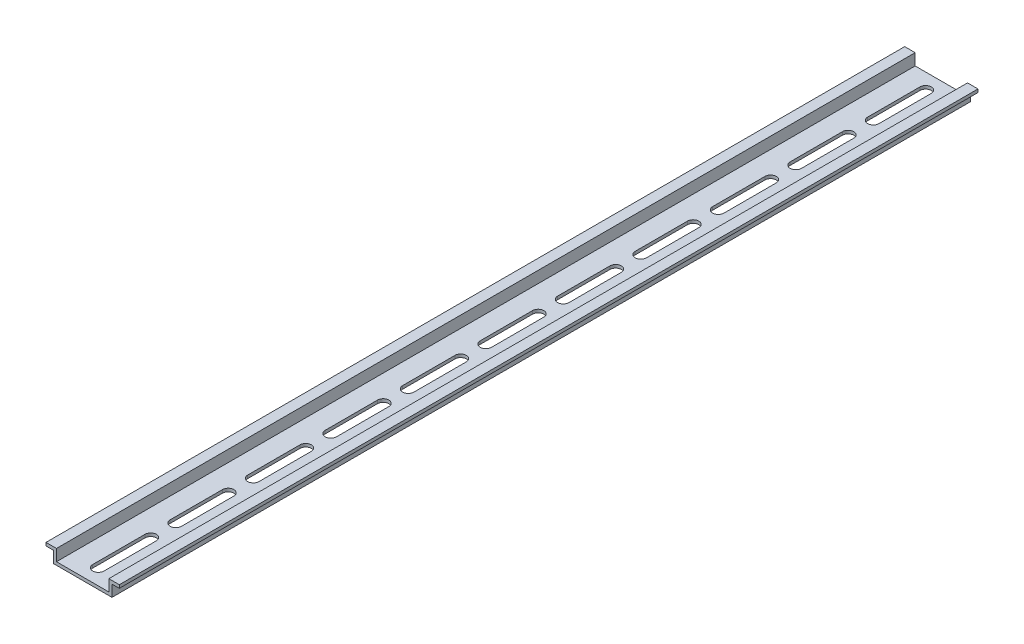
SolidWorks part; units mm, degrees
ref_plane "Alzado" through (0, 0, 0) normal (0, 0, 1) x (1, 0, 0)
ref_plane "Planta" through (0, 0, 0) normal (0, 1, 0) x (1, 0, 0)
ref_plane "Vista lateral" through (0, 0, 0) normal (1, 0, 0) x (0, 0, -1)
ref_plane "Plano1" through (0, -1.5, 0) normal (0, -1, 0) x (1, 0, 0)
sketch "Croquis1" plane through (0, -1.5, 0) normal (0, -1, 0) x (1, 0, 0)
  line L0 (-17.5, 0) -> (17.5, 0)
  line L1 (17.5, 0) -> (17.5, 410)
  line L2 (17.5, 410) -> (-17.5, 410)
  line L3 (-17.5, 410) -> (-17.5, 0)
extrude "Saliente-Extruir1" add sketch "Croquis1" against normal blind 7
sketch "Croquis2" plane through (0, 0, 410) normal (0, 0, 1) x (1, 0, 0)
  line L0 (-12.5, 5.5) -> (-12.5, 0)
  line L1 (-12.5, 0) -> (12.5, 0)
  line L2 (12.5, 0) -> (12.5, 5.5)
  line L3 (12.5, 5.5) -> (-12.5, 5.5)
extrude "Cortar-Extruir1" cut sketch "Croquis2" against normal through all
sketch "Croquis3" plane through (0, 0, 410) normal (0, 0, 1) x (1, 0, 0)
  line L0 (17.5, -1.5) -> (17.5, 4)
  line L1 (17.5, 4) -> (14, 4)
  line L2 (14, 4) -> (14, -1.5)
  line L3 (14, -1.5) -> (17.5, -1.5)
extrude "Cortar-Extruir2" cut sketch "Croquis3" against normal through all
sketch "Croquis4" plane through (0, 0, 410) normal (0, 0, 1) x (1, 0, 0)
  line L0 (-17.5, -1.5) -> (-14, -1.5)
  line L1 (-14, -1.5) -> (-14, 4)
  line L2 (-14, 4) -> (-17.5, 4)
  line L3 (-17.5, 4) -> (-17.5, -1.5)
extrude "Cortar-Extruir3" cut sketch "Croquis4" against normal through all
sketch "Croquis5" plane through (0, 0, 0) normal (0, 1, 0) x (-1, 0, 0)
  line L0 (-2.7, 402.5) -> (-2.7, 377.5)
  line L1 (2.7, 377.5) -> (2.7, 402.5)
  arc A0 (2.7, 402.5) -> (-2.7, 402.5) centre (0, 402.5) ccw
  arc A1 (-2.7, 377.5) -> (2.7, 377.5) centre (0, 377.5) ccw
extrude "Cortar-Extruir4" cut sketch "Croquis5" against normal through all
sketch "Croquis6" plane through (0, 0, 0) normal (0, 1, 0) x (-1, 0, 0)
  line L0 (-2.7, 365.5) -> (-2.7, 340.5)
  line L1 (2.7, 340.5) -> (2.7, 365.5)
  arc A0 (2.7, 365.5) -> (-2.7, 365.5) centre (0, 365.5) ccw
  arc A1 (-2.7, 340.5) -> (2.7, 340.5) centre (0, 340.5) ccw
extrude "Cortar-Extruir5" cut sketch "Croquis6" against normal through all
sketch "Croquis7" plane through (0, 0, 0) normal (0, 1, 0) x (-1, 0, 0)
  line L0 (-2.7, 328.5) -> (-2.7, 303.5)
  line L1 (2.7, 303.5) -> (2.7, 328.5)
  arc A0 (2.7, 328.5) -> (-2.7, 328.5) centre (0, 328.5) ccw
  arc A1 (-2.7, 303.5) -> (2.7, 303.5) centre (0, 303.5) ccw
extrude "Cortar-Extruir6" cut sketch "Croquis7" against normal through all
sketch "Croquis8" plane through (0, 0, 0) normal (0, 1, 0) x (-1, 0, 0)
  line L0 (-2.7, 291.5) -> (-2.7, 266.5)
  line L1 (2.7, 266.5) -> (2.7, 291.5)
  arc A0 (2.7, 291.5) -> (-2.7, 291.5) centre (0, 291.5) ccw
  arc A1 (-2.7, 266.5) -> (2.7, 266.5) centre (0, 266.5) ccw
extrude "Cortar-Extruir7" cut sketch "Croquis8" against normal through all
sketch "Croquis9" plane through (0, 0, 0) normal (0, 1, 0) x (-1, 0, 0)
  line L0 (-2.7, 254.5) -> (-2.7, 229.5)
  line L1 (2.7, 229.5) -> (2.7, 254.5)
  arc A0 (2.7, 254.5) -> (-2.7, 254.5) centre (0, 254.5) ccw
  arc A1 (-2.7, 229.5) -> (2.7, 229.5) centre (0, 229.5) ccw
extrude "Cortar-Extruir8" cut sketch "Croquis9" against normal through all
sketch "Croquis10" plane through (0, 0, 0) normal (0, 1, 0) x (-1, 0, 0)
  line L0 (-2.7, 217.5) -> (-2.7, 192.5)
  line L1 (2.7, 192.5) -> (2.7, 217.5)
  arc A0 (2.7, 217.5) -> (-2.7, 217.5) centre (0, 217.5) ccw
  arc A1 (-2.7, 192.5) -> (2.7, 192.5) centre (0, 192.5) ccw
extrude "Cortar-Extruir9" cut sketch "Croquis10" against normal through all
sketch "Croquis11" plane through (0, 0, 0) normal (0, 1, 0) x (-1, 0, 0)
  line L0 (-2.7, 180.5) -> (-2.7, 155.5)
  line L1 (2.7, 155.5) -> (2.7, 180.5)
  arc A0 (2.7, 180.5) -> (-2.7, 180.5) centre (0, 180.5) ccw
  arc A1 (-2.7, 155.5) -> (2.7, 155.5) centre (0, 155.5) ccw
extrude "Cortar-Extruir10" cut sketch "Croquis11" against normal through all
sketch "Croquis12" plane through (0, 0, 0) normal (0, 1, 0) x (-1, 0, 0)
  line L0 (-2.7, 143.5) -> (-2.7, 118.5)
  line L1 (2.7, 118.5) -> (2.7, 143.5)
  arc A0 (2.7, 143.5) -> (-2.7, 143.5) centre (0, 143.5) ccw
  arc A1 (-2.7, 118.5) -> (2.7, 118.5) centre (0, 118.5) ccw
extrude "Cortar-Extruir11" cut sketch "Croquis12" against normal through all
sketch "Croquis13" plane through (0, 0, 0) normal (0, 1, 0) x (-1, 0, 0)
  line L0 (-2.7, 106.5) -> (-2.7, 81.5)
  line L1 (2.7, 81.5) -> (2.7, 106.5)
  arc A0 (2.7, 106.5) -> (-2.7, 106.5) centre (0, 106.5) ccw
  arc A1 (-2.7, 81.5) -> (2.7, 81.5) centre (0, 81.5) ccw
extrude "Cortar-Extruir12" cut sketch "Croquis13" against normal through all
sketch "Croquis14" plane through (0, 0, 0) normal (0, 1, 0) x (-1, 0, 0)
  line L0 (-2.7, 69.5) -> (-2.7, 44.5)
  line L1 (2.7, 44.5) -> (2.7, 69.5)
  arc A0 (2.7, 69.5) -> (-2.7, 69.5) centre (0, 69.5) ccw
  arc A1 (-2.7, 44.5) -> (2.7, 44.5) centre (0, 44.5) ccw
extrude "Cortar-Extruir13" cut sketch "Croquis14" against normal through all
sketch "Croquis15" plane through (0, -1.5, 0) normal (0, -1, 0) x (1, 0, 0)
  line L0 (-2.7, 32.5) -> (-2.7, 7.5)
  line L1 (2.7, 7.5) -> (2.7, 32.5)
  arc A0 (2.7, 32.5) -> (-2.7, 32.5) centre (0, 32.5) ccw
  arc A1 (-2.7, 7.5) -> (2.7, 7.5) centre (0, 7.5) ccw
extrude "Cortar-Extruir14" cut sketch "Croquis15" against normal through all
